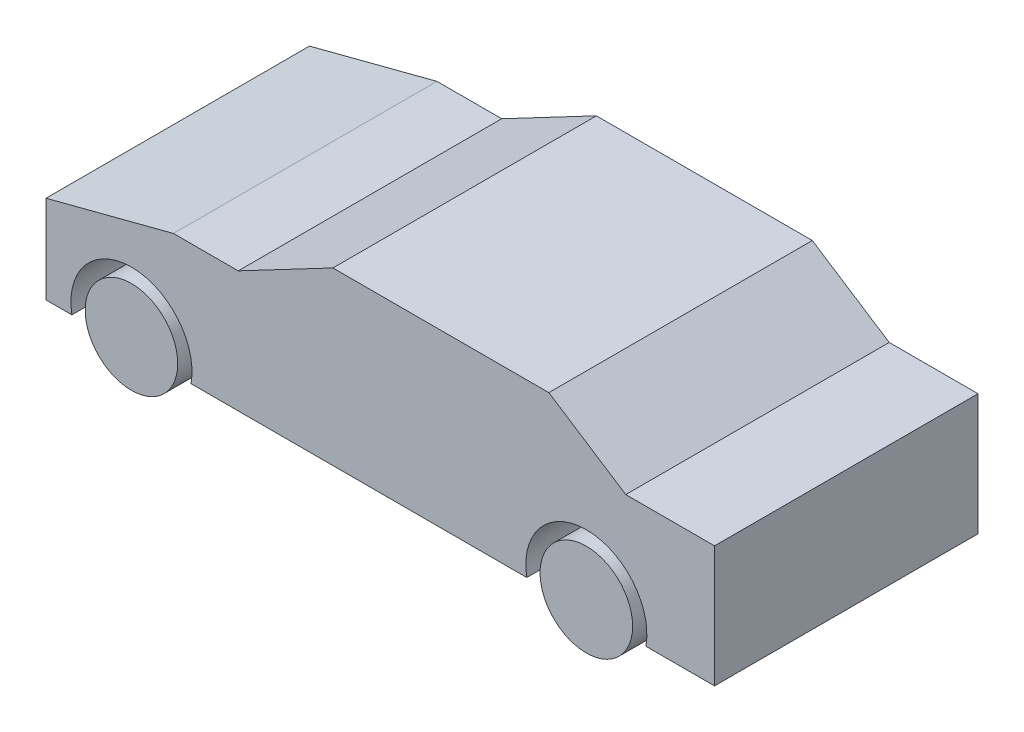
SolidWorks part; units mm, degrees
ref_plane "Front Plane" through (0, 0, 0) normal (0, 0, 1) x (1, 0, 0)
ref_plane "Top Plane" through (0, 0, 0) normal (0, 1, 0) x (1, 0, 0)
ref_plane "Right Plane" through (0, 0, 0) normal (1, 0, 0) x (0, 0, -1)
sketch "Sketch1" plane through (0, 0, 0) normal (0, 0, 1) x (1, 0, 0)
  line L0 (0, -574.3008) -> (895.3088, -341.1864)
  line L1 (2014.431, 8.8136) -> (3530.6479, 8.8136)
  line L4 (4694, -341.1864) -> (4694, -1193)
  line L5 (895.3088, -341.1864) -> (1349.7879, -341.1864)
  line L6 (0, -574.3008) -> (0, -1193)
  line L7 (0, -1193) -> (181.67, -1193)
  line L8 (4694, -341.1864) -> (4694, -1193)
  line L9 (1349.7879, -341.1864) -> (2014.431, 8.8136)
  line L10 (3530.6479, 8.8136) -> (4070.6704, -341.1864)
  line L11 (0, -574.3008) -> (0, -1193)
  line L12 (4070.6704, -341.1864) -> (4694, -341.1864)
  line L14 (4212.33, -1193) -> (4694, -1193)
  line L15 (1018.33, -1193) -> (3375.67, -1193)
  circle A0 centre (600, -1118) radius 325
  circle A1 centre (3794, -1118) radius 325
  arc A2 (1018.33, -1193) -> (181.67, -1193) centre (600, -1118) ccw
  arc A3 (4212.33, -1193) -> (3375.67, -1193) centre (3794, -1118) ccw
  point P1 (0, -574.3008)
  point P2 (895.3088, -341.1864)
  dimension "D3" = 650
  dimension "D4" = 650
  dimension "D9" = 850
  dimension "D10" = 850
  dimension "D6" = 900
  dimension "D8" = 350
extrude "Boss-Extrude1" add sketch "Sketch1" along normal blind 1850 contours A3 L14 L4 L12 L10 L1 L9 L5 L0 L6 L7 A2 L15 | A0 | A1
